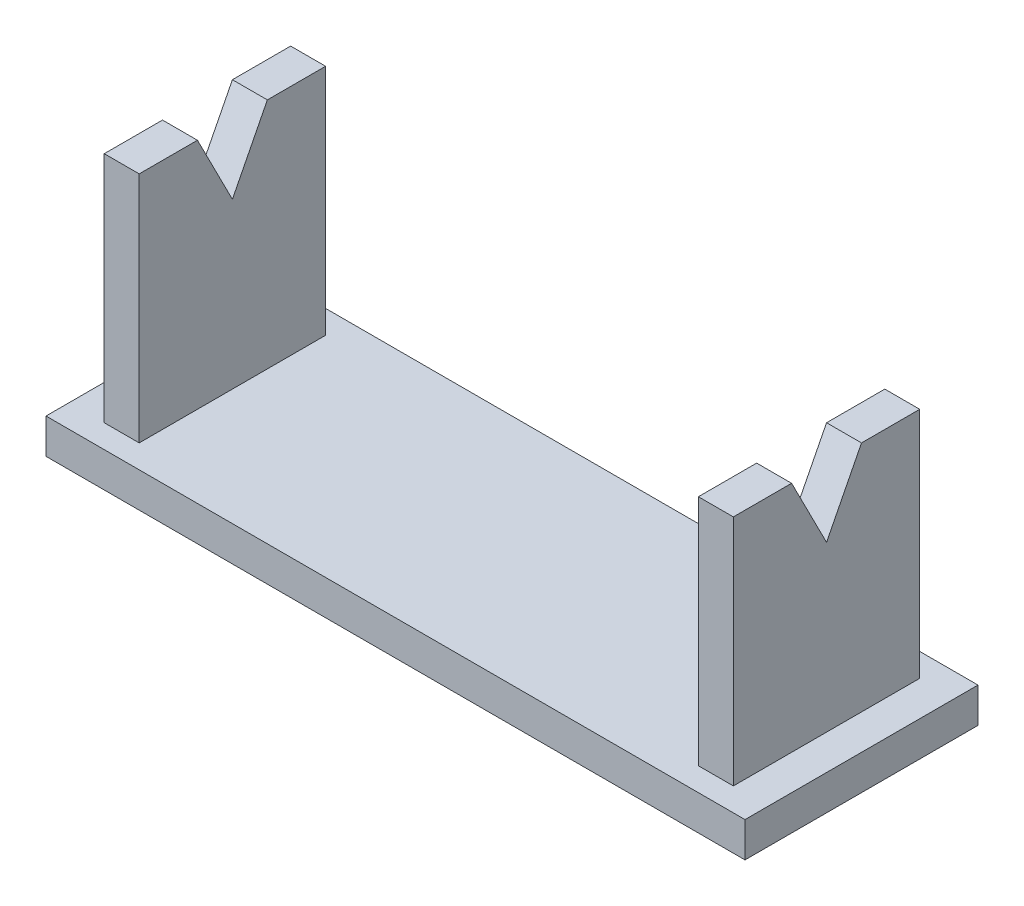
SolidWorks part; units mm, degrees
ref_plane "Спереди" through (0, 0, 0) normal (0, 0, 1) x (1, 0, 0)
ref_plane "Сверху" through (0, 0, 0) normal (0, 1, 0) x (1, 0, 0)
ref_plane "Справа" through (0, 0, 0) normal (1, 0, 0) x (0, 0, -1)
other "Configuration Table"
sketch "Эскиз1" plane through (0, 0, 0) normal (0, 1, 0) x (1, 0, 0)
  line L0 (0, 0) -> (60, 0)
  line L1 (0, 0) -> (0, 20)
  line L2 (0, 20) -> (60, 20)
  line L3 (60, 20) -> (60, 0)
  dimension "D1" = 60
  dimension "D2" = 20
extrude "Основание" add sketch "Эскиз1" along normal blind 3
sketch "Эскиз3" plane through (0, 3, 0) normal (0, 1, 0) x (1, 0, 0)
  line L0 (0, 20) -> (0, 0) construction
  line L1 (3, 18) -> (6, 18)
  line L2 (3, 18) -> (3, 2)
  line L3 (3, 2) -> (6, 2)
  line L4 (6, 18) -> (6, 2)
  line L5 (60, 20) -> (0, 20) construction
  line L6 (0, 10) -> (60, 10) construction
  line L7 (60, 0) -> (60, 20) construction
  line L8 (30, 10) -> (30, 25.7032) construction
  line L9 (54, 18) -> (54, 2)
  line L10 (57, 2) -> (54, 2)
  line L11 (57, 18) -> (57, 2)
  line L12 (57, 18) -> (54, 18)
  dimension "D1" = 3
  dimension "D2" = 3
  dimension "D3" = 2
  dimension "D4" = 16
extrude "Бобышка-Вытянуть3" add sketch "Эскиз3" along normal blind 20
sketch "Эскиз13" plane through (57, 0, 0) normal (1, 0, 0) x (0, 0, -1)
  line L0 (2, 23) -> (7, 23) construction
  line L1 (2, 23) -> (18, 23) construction
  line L2 (7, 23) -> (13, 23) construction
  line L3 (13, 23) -> (10, 17.1102) construction
  line L4 (10, 17.1102) -> (7, 23) construction
  line L5 (7, 23) -> (-20.2727, 21.5262) construction
  line L6 (7, 23) -> (10, 17.1102)
  line L7 (10, 17.1102) -> (13, 23)
  line L8 (13, 23) -> (7, 23)
extrude "Вырез-Вытянуть4" cut sketch "Эскиз13" against normal through all both and the other way through all
